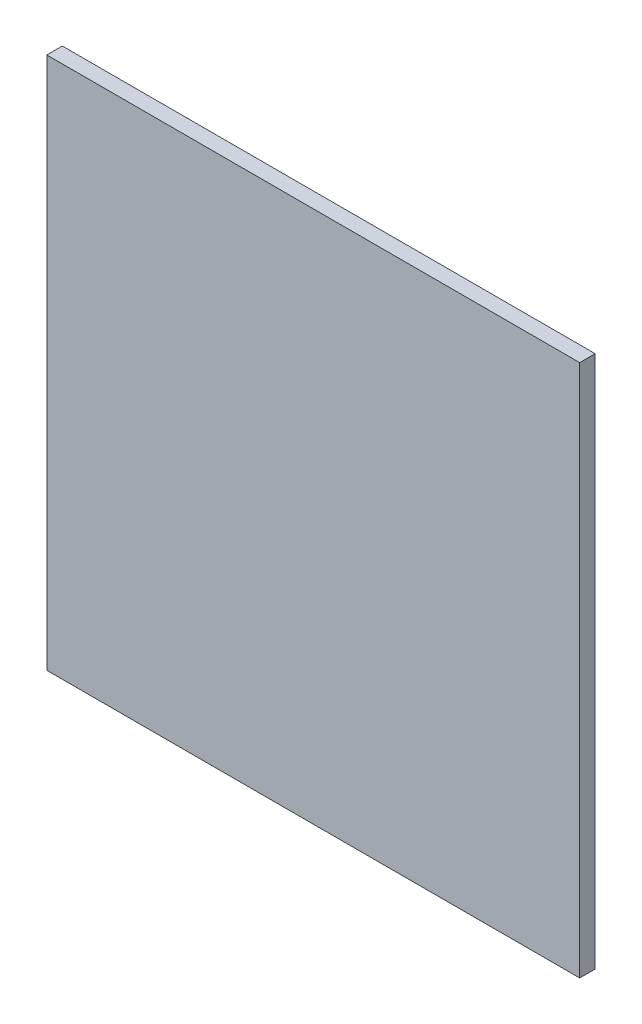
SolidWorks part; units mm, degrees
ref_plane "Front Plane" through (0, 0, 0) normal (0, 0, 1) x (1, 0, 0)
ref_plane "Top Plane" through (0, 0, 0) normal (0, 1, 0) x (1, 0, 0)
ref_plane "Right Plane" through (0, 0, 0) normal (1, 0, 0) x (0, 0, -1)
sketch "Sketch1" plane through (0, 0, 0) normal (0, 0, 1) x (1, 0, 0)
  line L1 (-35.1975, 58.106) -> (50.8025, 58.106)
  line L2 (-35.1975, 58.106) -> (-35.1975, -27.894)
  line L3 (-35.1975, -27.894) -> (50.8025, -27.894)
  line L4 (50.8025, 58.106) -> (50.8025, -27.894)
extrude "Boss-Extrude1" add sketch "Sketch1" along normal blind 2.5
